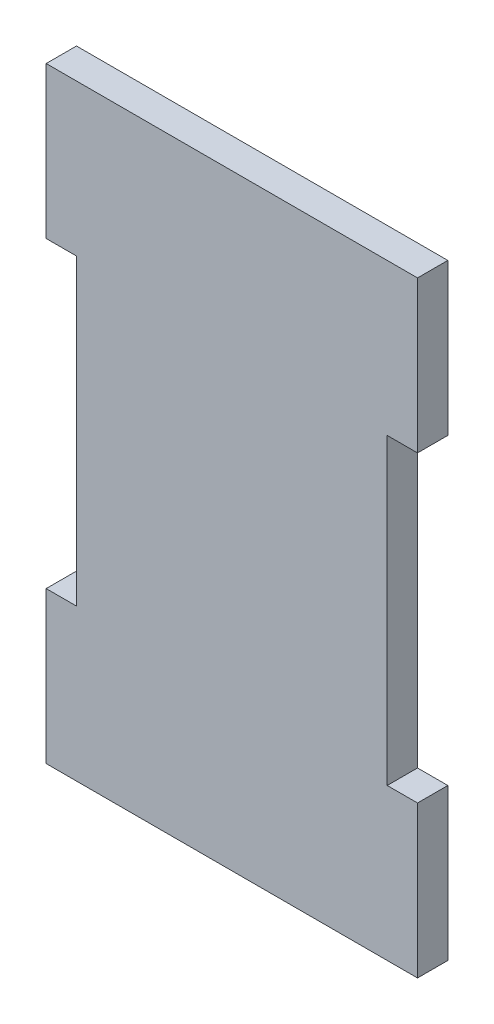
SolidWorks part; units mm, degrees
ref_plane "Front Plane" through (0, 0, 0) normal (0, 0, 1) x (1, 0, 0)
ref_plane "Top Plane" through (0, 0, 0) normal (0, 1, 0) x (1, 0, 0)
ref_plane "Right Plane" through (0, 0, 0) normal (1, 0, 0) x (0, 0, -1)
sketch "Sketch2" plane through (0, 0, 0) normal (0, 0, 1) x (1, 0, 0)
  line L1 (26.035, -50.8) -> (-26.035, -50.8)
  line L2 (26.035, -50.8) -> (26.035, 50.8)
  line L3 (26.035, 50.8) -> (-26.035, 50.8)
  line L4 (-26.035, -50.8) -> (-26.035, 50.8)
  line L5 (26.035, -50.8) -> (-26.035, 50.8) construction
  line L6 (26.035, 50.8) -> (-26.035, -50.8) construction
  line L7 (-26.035, 50.8) -> (-31.115, 50.8)
  line L8 (-26.035, 50.8) -> (-26.035, 25.4)
  line L9 (-26.035, 25.4) -> (-31.115, 25.4)
  line L10 (-31.115, 50.8) -> (-31.115, 25.4)
  line L11 (-26.035, -50.8) -> (-31.115, -50.8)
  line L12 (-26.035, -50.8) -> (-26.035, -25.4)
  line L13 (-26.035, -25.4) -> (-31.115, -25.4)
  line L14 (-31.115, -50.8) -> (-31.115, -25.4)
  line L15 (26.035, -50.8) -> (31.115, -50.8)
  line L16 (26.035, -50.8) -> (26.035, -25.4)
  line L17 (26.035, -25.4) -> (31.115, -25.4)
  line L18 (31.115, -50.8) -> (31.115, -25.4)
  line L19 (26.035, 50.8) -> (31.115, 50.8)
  line L20 (26.035, 50.8) -> (26.035, 25.4)
  line L21 (26.035, 25.4) -> (31.115, 25.4)
  line L22 (31.115, 50.8) -> (31.115, 25.4)
  point P0 (0, 0)
  dimension "D1" = 101.6
  dimension "D2" = 52.07
  dimension "D3" = 5.08
  dimension "D4" = 25.4
extrude "Boss-Extrude1" add sketch "Sketch2" along normal blind 5.08 contours L4 L1 L2 L3 | L7 L10 L9 L4 | L14 L11 L4 L13 | L15 L18 L17 L2 | L22 L19 L2 L21
